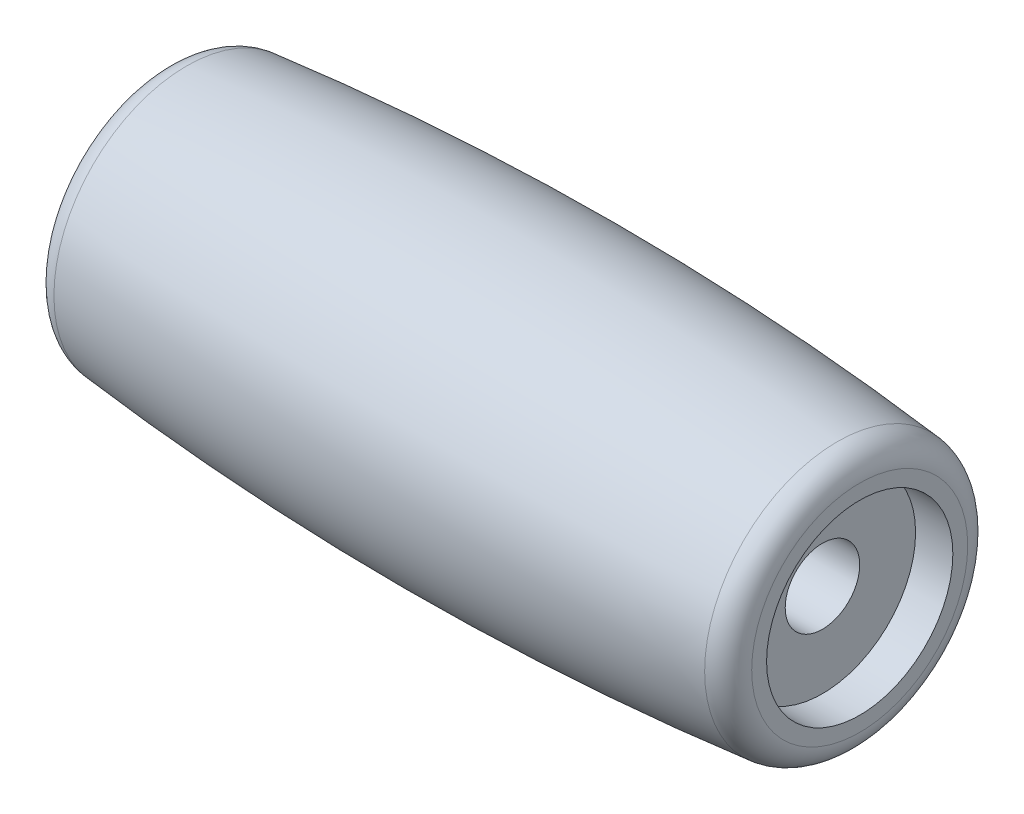
SolidWorks part; units mm, degrees
ref_plane "Front Plane" through (0, 0, 0) normal (0, 0, 1) x (1, 0, 0)
ref_plane "Top Plane" through (0, 0, 0) normal (0, 1, 0) x (1, 0, 0)
ref_plane "Right Plane" through (0, 0, 0) normal (1, 0, 0) x (0, 0, -1)
sketch "Sketch1" plane through (0, 0, 0) normal (0, 0, 1) x (1, 0, 0)
  line L0 (0, 6) -> (0, 0) construction
  line L1 (-13.6318, 0) -> (13.6318, 0) construction
  line L2 (-12.5, 1.5) -> (12.5, 1.5)
  line L3 (12.5, 1.5) -> (12.5, 3.75)
  line L4 (12.5, 3.75) -> (14, 3.75)
  line L5 (14, 3.75) -> (14, 4.3486)
  line L6 (-14, 3.75) -> (-14, 4.3486)
  line L7 (-12.5, 3.75) -> (-14, 3.75)
  line L8 (-12.5, 1.5) -> (-12.5, 3.75)
  arc A0 (-13.1, 5.3436) -> (13.1, 5.3436) centre (0, -125.0417) cw
  arc A1 (14, 4.3486) -> (13.1, 5.3436) centre (13, 4.3486) ccw
  arc A2 (-14, 4.3486) -> (-13.1, 5.3436) centre (-13, 4.3486) cw
  point P14 (0, 1.5)
  point P21 (14, 5.25)
  point P24 (-14, 5.25)
  dimension "D7" = 1
  dimension "D1" = 1.5
  dimension "D2" = 3.75
  dimension "D3" = 1.5
  dimension "D4" = 1.5
  dimension "D5" = 14
  dimension "D6" = 6
revolve "Revolve1" add sketch "Sketch1" angle 360 about L1
scale "Scale1" scale about origin uniform scaling yes scale factor 1.667
